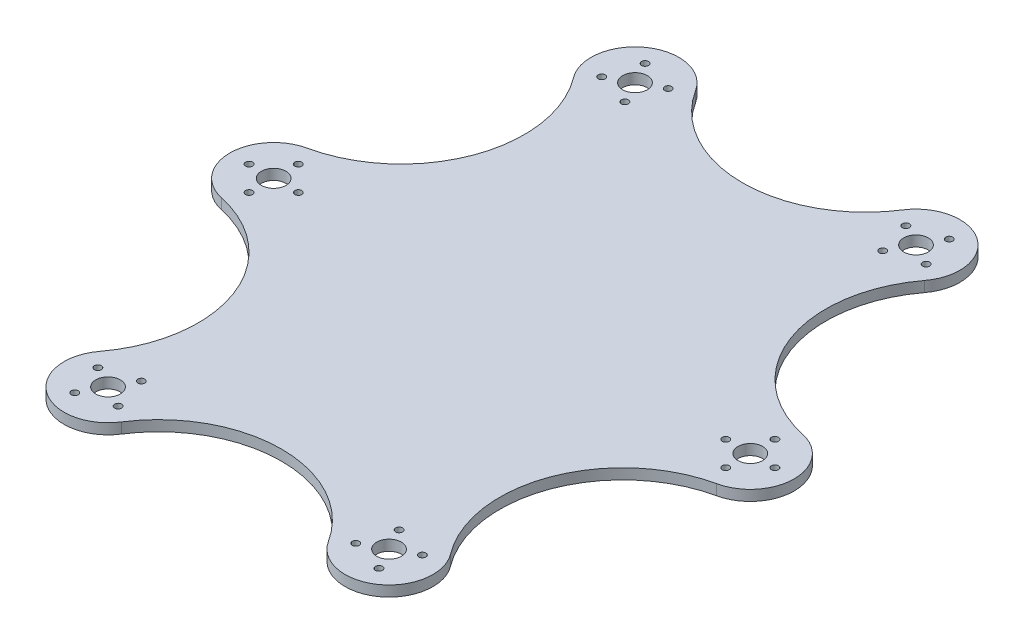
SolidWorks part; units mm, degrees
material "1345 Alloy"
ref_plane "Front Plane" through (0, 0, 0) normal (0, 0, 1) x (1, 0, 0)
ref_plane "Top Plane" through (0, 0, 0) normal (0, 1, 0) x (1, 0, 0)
ref_plane "Right Plane" through (0, 0, 0) normal (1, 0, 0) x (0, 0, -1)
sketch "Sketch2" plane through (0, 0, 0) normal (0, 1, 0) x (1, 0, 0)
  circle A0 centre (-40, 75) radius 3.5
  arc A1 (-29.4737, 81.7414) -> (-49.9831, 67.4775) centre (-40, 75) ccw
  arc A2 (-70.4959, 12.2143) -> (-70.4959, -12.2143) centre (-67.8388, 0) ccw
  circle A3 centre (-67.8388, 0) radius 3.5
  circle A4 centre (-40, -75) radius 3.5
  arc A5 (-49.9831, -67.4775) -> (-29.4737, -81.7414) centre (-40, -75) ccw
  circle A6 centre (40, -75) radius 3.5
  arc A7 (29.4737, -81.7414) -> (49.9831, -67.4775) centre (40, -75) ccw
  circle A8 centre (67.8388, 0) radius 3.5
  arc A9 (70.4959, -12.2143) -> (70.4959, 12.2143) centre (67.8388, 0) ccw
  circle A10 centre (40, 75) radius 3.5
  arc A11 (49.9831, 67.4775) -> (29.4737, 81.7414) centre (40, 75) ccw
  arc A12 (-29.4737, 81.7414) -> (29.4737, 81.7414) centre (0, 100.6174) ccw
  arc A13 (-70.4959, 12.2143) -> (-49.9831, 67.4775) centre (-77.9357, 46.4145) ccw
  arc A14 (-49.9831, -67.4775) -> (-70.4959, -12.2143) centre (-77.9357, -46.4145) ccw
  arc A15 (70.4959, -12.2143) -> (49.9831, -67.4775) centre (77.9357, -46.4145) ccw
  arc A16 (49.9831, 67.4775) -> (70.4959, 12.2143) centre (77.9357, 46.4145) ccw
  arc A17 (29.4737, -81.7414) -> (-29.4737, -81.7414) centre (0, -100.6174) ccw
  circle A18 centre (-36.7059, 68.8235) radius 1
  circle A19 centre (-33.8235, 78.2941) radius 1
  circle A20 centre (-43.2941, 81.1765) radius 1
  circle A21 centre (-46.1765, 71.7059) radius 1
  circle A22 centre (-36.7059, -68.8235) radius 1
  circle A23 centre (-33.8235, -78.2941) radius 1
  circle A24 centre (-43.2941, -81.1765) radius 1
  circle A25 centre (-46.1765, -71.7059) radius 1
  circle A26 centre (-60.8388, 0) radius 1
  circle A27 centre (-67.8388, 7) radius 1
  circle A28 centre (-67.8388, -7) radius 1
  circle A29 centre (-74.8388, 0) radius 1
  circle A30 centre (43.2941, -81.1765) radius 1
  circle A31 centre (33.8235, -78.2941) radius 1
  circle A32 centre (46.1765, -71.7059) radius 1
  circle A33 centre (36.7059, -68.8235) radius 1
  circle A34 centre (67.8388, -7) radius 1
  circle A35 centre (60.8388, 0) radius 1
  circle A36 centre (74.8388, 0) radius 1
  circle A37 centre (67.8388, 7) radius 1
  circle A38 centre (36.7059, 68.8235) radius 1
  circle A39 centre (46.1765, 71.7059) radius 1
  circle A40 centre (33.8235, 78.2941) radius 1
  circle A41 centre (43.2941, 81.1765) radius 1
  dimension "D9" = 7
  dimension "D10" = 25
  dimension "D11" = 25
  dimension "D12" = 7
  dimension "D13" = 25
  dimension "D14" = 7
  dimension "D15" = 25
  dimension "D16" = 7
  dimension "D17" = 25
  dimension "D18" = 7
  dimension "D19" = 25
  dimension "D20" = 7
  dimension "D21" = 70
  dimension "D22" = 2
  dimension "D23" = 2
  dimension "D26" = 2
  dimension "D27" = 2
  dimension "D2" = 80
  dimension "D3" = 150
  dimension "D5" = 80
  dimension "D6" = 80
  dimension "D7" = 80
  dimension "D8" = 80
  dimension "D24" = 7
  dimension "D25" = 7
  dimension "D28" = 7
  dimension "D29" = 7
extrude "Boss-Extrude1" add sketch "Sketch2" along normal blind 3
